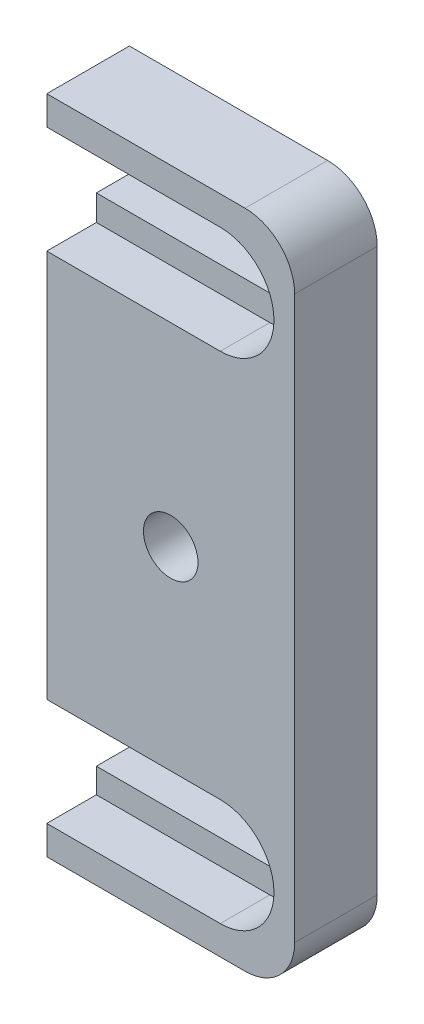
SolidWorks part; units mm, degrees
ref_plane "Front Plane" through (0, 0, 0) normal (0, 0, 1) x (1, 0, 0)
ref_plane "Top Plane" through (0, 0, 0) normal (0, 1, 0) x (1, 0, 0)
ref_plane "Right Plane" through (0, 0, 0) normal (1, 0, 0) x (0, 0, -1)
ref_plane "Plane1" through (0, 0, 5) normal (0, 0, 1) x (1, 0, 0)
sketch "Sketch1" plane through (0, 0, 5) normal (0, 0, 1) x (1, 0, 0)
  line L0 (15, 0) -> (0, 0)
  line L1 (0, 0) -> (0, -40)
  line L2 (0, -40) -> (15, -40)
  line L3 (15, -40) -> (15, 0)
extrude "Boss-Extrude1" add sketch "Sketch1" against normal blind 5
sketch "Sketch2" plane through (0, 0, 5) normal (0, 0, 1) x (1, 0, 0)
  line L0 (0, -8.25) -> (10.5, -8.25)
  line L1 (10.5, -1.75) -> (0, -1.75)
  line L2 (0, -1.75) -> (0, -8.25)
  arc A0 (10.5, -8.25) -> (10.5, -1.75) centre (10.5, -5) ccw
extrude "Cut-Extrude1" cut sketch "Sketch2" against normal blind 3
sketch "Sketch3" plane through (0, 0, 2) normal (0, 0, 1) x (1, 0, 0)
  line L0 (0, -3.3) -> (0, -6.7)
  line L1 (0, -6.7) -> (10.5, -6.7)
  line L2 (10.5, -3.3) -> (0, -3.3)
  arc A0 (10.5, -6.7) -> (10.5, -3.3) centre (10.5, -5) ccw
extrude "Cut-Extrude2" cut sketch "Sketch3" against normal through all
sketch "Sketch4" plane through (0, 0, 5) normal (0, 0, 1) x (1, 0, 0)
  line L0 (0, -38.25) -> (10.5, -38.25)
  line L1 (10.5, -31.75) -> (0, -31.75)
  line L2 (0, -31.75) -> (0, -38.25)
  arc A0 (10.5, -38.25) -> (10.5, -31.75) centre (10.5, -35) ccw
extrude "Cut-Extrude3" cut sketch "Sketch4" against normal blind 3
sketch "Sketch5" plane through (0, 0, 0) normal (0, 0, -1) x (-1, 0, 0)
  line L0 (0, -36.75) -> (0, -33.25)
  line L1 (0, -33.25) -> (-10.5, -33.25)
  line L2 (-10.5, -36.75) -> (0, -36.75)
  arc A0 (-10.5, -33.25) -> (-10.5, -36.75) centre (-10.5, -35) ccw
extrude "Cut-Extrude4" cut sketch "Sketch5" against normal through all
hole_wizard "#4 Clearance Hole1" positions "Sketch7" profile "Sketch6" hole size "#4" standard "ANSI Inch"
sketch "Sketch7" plane through (0, 0, 5) normal (0, 0, 1) x (1, 0, 0)
  point P0 (7.5, -20)
sketch "Sketch6" plane through (7.5, -20, 5) normal (1, 0, 0) x (0, -1, 0)
  line L0 (0, 0) -> (0, 5)
  line L1 (0, 5) -> (1.65, 5)
  line L2 (1.65, 5) -> (1.65, 0)
  line L5 (1.65, 0) -> (0, 0)
  line L11 (0, -6.35) -> (0, 107.95) construction
  dimension "Thru Hole Dia." = 3.3
  dimension "Thru Hole Depth" = 5
fillet "Fillet1" radius 3 2 edges at (15, -40, 2.5) (15, 0, 2.5)
